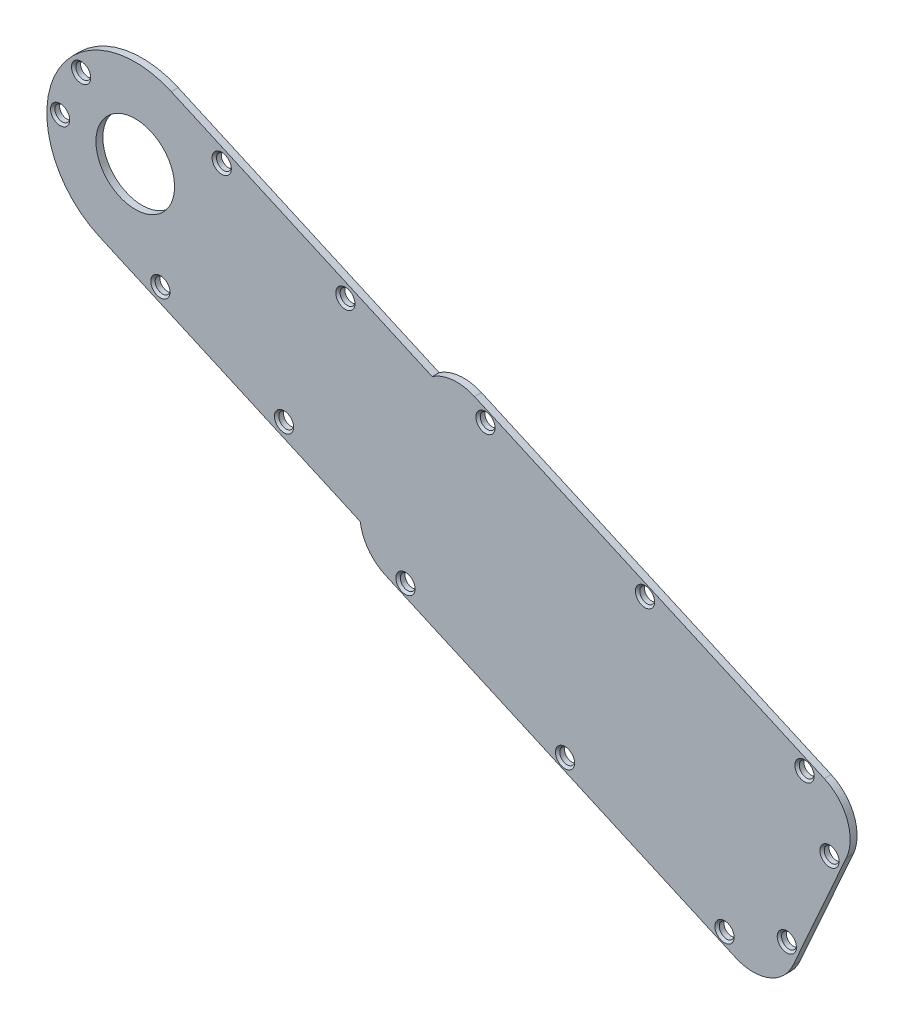
SolidWorks part; units mm, degrees
ref_plane "Front Plane" through (0, 0, 0) normal (0, 0, 1) x (1, 0, 0)
ref_plane "Top Plane" through (0, 0, 0) normal (0, 1, 0) x (1, 0, 0)
ref_plane "Right Plane" through (0, 0, 0) normal (1, 0, 0) x (0, 0, -1)
ref_plane "Plane1" through (0, 0, 1.5875) normal (0, 0, 1) x (1, 0, 0)
sketch "Sketch1" plane through (0, 0, 1.5875) normal (0, 0, 1) x (1, 0, 0)
  line L0 (-122.3733, 49.5916) -> (-33.1379, 9.8129)
  line L1 (-33.1379, 9.8129) -> (-12.7803, 55.4809)
  line L2 (-12.7803, 55.4809) -> (-102.0156, 95.2596)
  line L3 (-111.7232, 94.3865) -> (-171.498, 121.0325)
  line L4 (-187.9877, 84.0414) -> (-128.2129, 57.3954)
  arc A0 (-102.0156, 95.2596) -> (-111.7232, 94.3865) centre (-106.0872, 86.126) ccw
  arc A1 (-171.498, 121.0325) -> (-187.9877, 84.0414) centre (-179.7428, 102.5369) ccw
  arc A2 (-128.2129, 57.3954) -> (-122.3733, 49.5916) centre (-118.3017, 58.7252) ccw
extrude "Boss-Extrude1" add sketch "Sketch1" against normal blind 1.5875
hole_wizard "#4 Clearance Hole1" positions "Sketch3" profile "Sketch2" hole size "#4" standard "ANSI Inch"
sketch "Sketch3" plane through (0, 0, 1.5875) normal (0, 0, 1) x (1, 0, 0)
  point P0 (-99.5171, 91.4087)
  point P1 (-62.9827, 75.1226)
  point P2 (-26.4483, 58.8365)
  point P3 (-20.7221, 44.7879)
  point P4 (-30.4937, 22.8673)
  point P5 (-44.7701, 17.7353)
  point P6 (-81.3045, 34.0214)
  point P7 (-117.8389, 50.3075)
  point P8 (-131.6182, 99.9706)
  point P9 (-145.665, 68.4596)
  point P10 (-173.9792, 81.0813)
  point P11 (-159.9324, 112.5923)
  point P12 (-192.146, 114.5254)
  point P13 (-196.9503, 103.7481)
sketch "Sketch2" plane through (-99.5171, 91.4087, 1.5875) normal (1, 0, 0) x (0, -1, 0)
  line L0 (0, 0) -> (0, 1.5875)
  line L1 (0, 1.5875) -> (1.7, 1.5875)
  line L2 (1.7, 1.5875) -> (1.7, 0)
  line L5 (1.7, 0) -> (0, 0)
  line L11 (0, -6.35) -> (0, 107.95) construction
  dimension "Thru Hole Dia." = 3.4
  dimension "Thru Hole Depth" = 1.5875
hole_wizard "Hole1" positions "Sketch5" profile "Sketch4" legacy
sketch "Sketch5" plane through (0, 0, 0) normal (0, 0, -1) x (-1, 0, 0)
  point P0 (179.7428, 102.5369)
sketch "Sketch4" plane through (-179.7428, 102.5369, 0) normal (1, 0, 0) x (0, 1, 0)
  line L0 (0, 0) -> (0, 1.5875)
  line L1 (0, 1.5875) -> (9, 1.5875)
  line L2 (9, 1.5875) -> (9, 0)
  line L3 (9, 0) -> (0, 0)
  line L4 (0, 110) -> (0, -10) construction
  dimension "Diameter" = 18
  dimension "Depth" = 1.5875
chamfer "Chamfer1" distance 0.5 angle 45 14 edges at (-158.2324, 112.5923, 1.5875) (-28.7937, 22.8673, 1.5875) (-195.2503, 103.7481, 1.5875) (-43.0701, 17.7353, 1.5875) (-172.2792, 81.0813, 1.5875) (-79.6045, 34.0214, 1.5875) (-190.446, 114.5254, 1.5875) (-61.2827, 75.1226, 1.5875) (-19.0221, 44.7879, 1.5875) (-24.7483, 58.8365, 1.5875) (-143.965, 68.4596, 1.5875) (-116.1389, 50.3075, 1.5875) (-97.8171, 91.4087, 1.5875) (-129.9182, 99.9706, 1.5875)
fillet "Fillet1" radius 10 2 edges at (-12.7803, 55.4809, 0.7937) (-33.1379, 9.8129, 0.7937)
